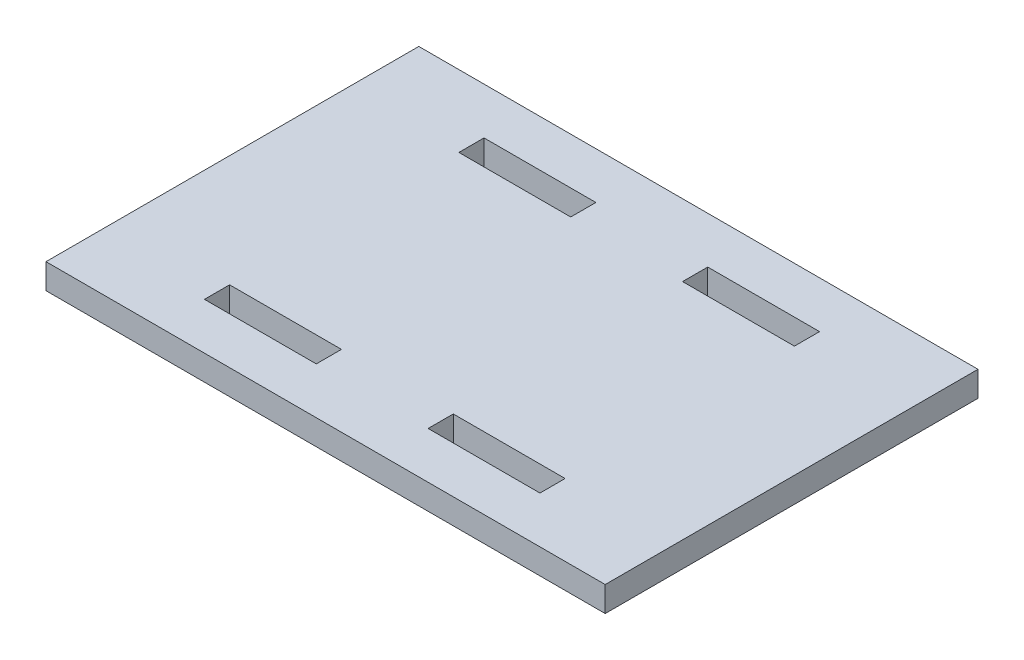
SolidWorks part; units mm, degrees
ref_plane "Ön Düzlem" through (0, 0, 0) normal (0, 0, 1) x (1, 0, 0)
ref_plane "Üst Düzlem" through (0, 0, 0) normal (0, 1, 0) x (1, 0, 0)
ref_plane "Sağ Düzlem" through (0, 0, 0) normal (1, 0, 0) x (0, 0, -1)
sketch "Sketch1" plane through (0, 0, 0) normal (0, 1, 0) x (1, 0, 0)
  line L0 (30, 20) -> (30, -20)
  line L1 (30, -20) -> (-30, -20)
  line L3 (30, 20) -> (-30, 20)
  line L4 (-30, -20) -> (-30, 20)
  line L5 (-6, 15) -> (-6, 12.3)
  line L6 (6, 15) -> (6, 12.3)
  line L8 (18, -15) -> (18, -12.3)
  line L9 (18, 12.3) -> (6, 12.3)
  line L11 (18, 15) -> (6, 15)
  line L12 (18, -15) -> (6, -15)
  line L13 (-6, 15) -> (-18, 15)
  line L14 (-6, 12.3) -> (-18, 12.3)
  line L15 (-18, 15) -> (-18, 12.3)
  line L16 (18, 15) -> (18, 12.3)
  line L17 (6, -15) -> (6, -12.3)
  line L18 (18, -12.3) -> (6, -12.3)
  line L19 (-6, -15) -> (-18, -15)
  line L20 (-6, -15) -> (-6, -12.3)
  line L21 (-6, -12.3) -> (-18, -12.3)
  line L22 (-18, -15) -> (-18, -12.3)
  point P0 (0, 0)
  dimension "D1" = 60
  dimension "D2" = 40
extrude "Boss-Extrude1" add sketch "Sketch1" against normal blind 2.7
